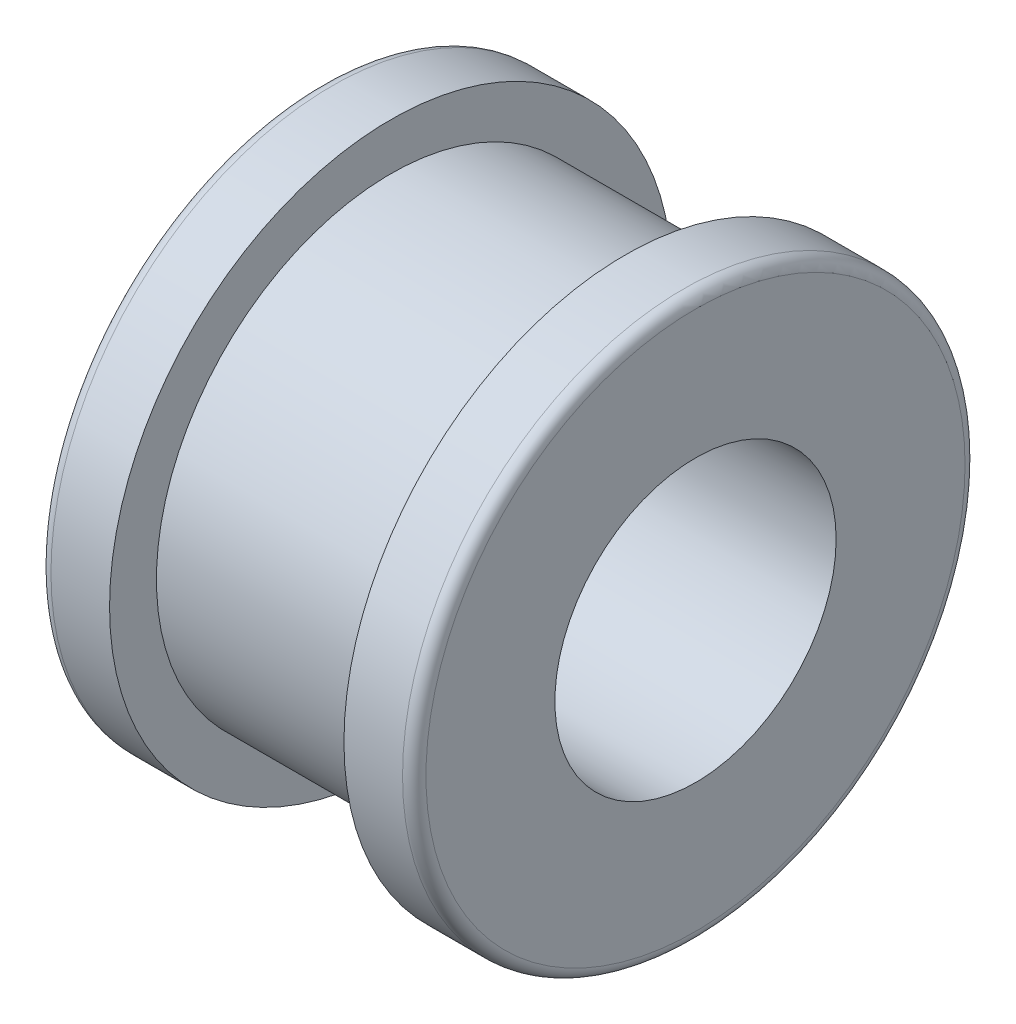
SolidWorks part; units mm, degrees
ref_plane "前视基准面" through (0, 0, 0) normal (0, 0, 1) x (1, 0, 0)
ref_plane "上视基准面" through (0, 0, 0) normal (0, 1, 0) x (1, 0, 0)
ref_plane "右视基准面" through (0, 0, 0) normal (1, 0, 0) x (0, 0, -1)
other "Configuration Table"
sketch "草图2" plane through (0, 0, 0) normal (1, 0, 0) x (0, 0, -1)
  circle A0 centre (0, 0) radius 12
extrude "凸台-拉伸1" add sketch "草图2" along normal mid plane 16
sketch "草图3" plane through (0, 0, 0) normal (1, 0, 0) x (0, 0, -1)
  circle A1 centre (0, 0) radius 12 construction
  circle A2 centre (0, 0) radius 10
  circle A3 centre (0, 0) radius 10
  circle A4 centre (0, 0) radius 12
  dimension "D1" = 2
extrude "切除-拉伸1" cut sketch "草图3" against normal mid plane 10
sketch "草图4" plane through (0, 0, 0) normal (1, 0, 0) x (0, 0, -1)
  circle A0 centre (0, 0) radius 6
  dimension "D1" = 12
extrude "切除-拉伸2" cut sketch "草图4" against normal through all both and the other way through all
fillet "圆角1" radius 0.5 2 edges at (8, 0, -12) (-8, 0, -12)
sketch "草图5" plane through (0, 0, 0) normal (0, 1, 0) x (1, 0, 0)
  circle A0 centre (0, 0) radius 1
extrude "切除-拉伸3" cut sketch "草图5" against normal blind 10
